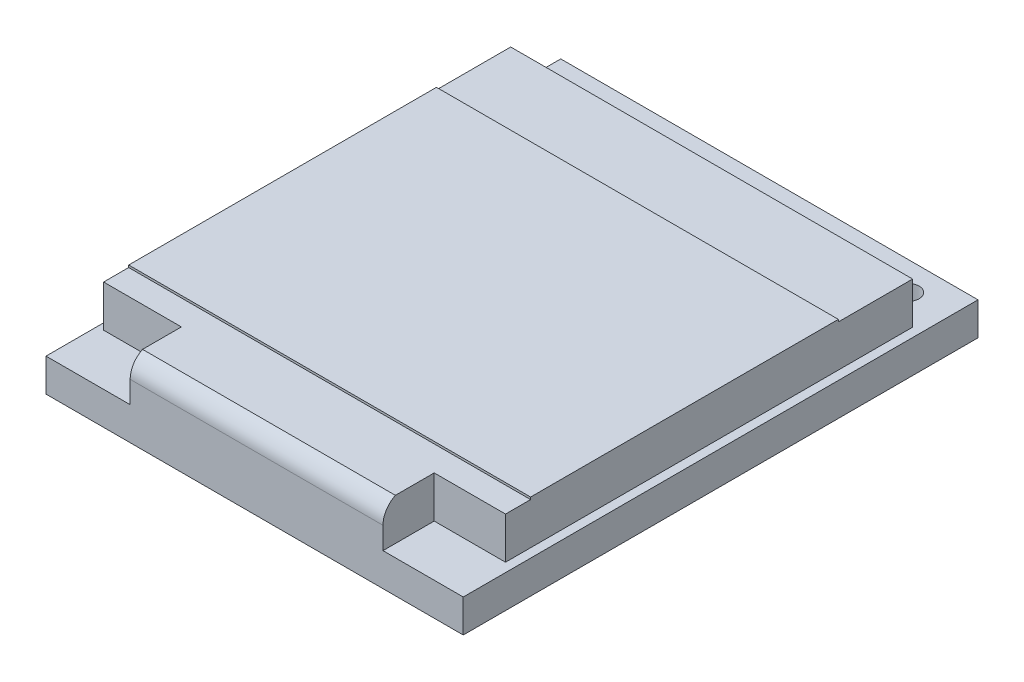
SolidWorks part; units mm, degrees
ref_plane "Front Plane" through (0, 0, 0) normal (0, 0, 1) x (1, 0, 0)
ref_plane "Top Plane" through (0, 0, 0) normal (0, 1, 0) x (1, 0, 0)
ref_plane "Right Plane" through (0, 0, 0) normal (1, 0, 0) x (0, 0, -1)
sketch "Sketch1" plane through (0, 0, 0) normal (0, 1, 0) x (1, 0, 0)
  line L0 (1.88, -1.3) -> (4.42, -1.3) construction
  line L1 (0, 0) -> (19, 0)
  line L2 (0, 0) -> (0, -23.44)
  line L3 (0, -23.44) -> (19, -23.44)
  line L4 (19, 0) -> (19, -23.44)
  circle A0 centre (1.88, -1.3) radius 0.5
  circle A1 centre (4.42, -1.3) radius 0.5
  circle A2 centre (6.96, -1.3) radius 0.5
  circle A3 centre (9.5, -1.3) radius 0.5
  circle A4 centre (12.04, -1.3) radius 0.5
  circle A5 centre (14.58, -1.3) radius 0.5
  circle A6 centre (17.12, -1.3) radius 0.5
  dimension "D3" = 7
  dimension "D5" = 1
  dimension "D1" = 19
  dimension "D2" = 23.44
  dimension "D4" = 2.54
  dimension "D6" = 1.88
  dimension "D7" = 1.3
extrude "Boss-Extrude1" add sketch "Sketch1" along normal blind 1.5
sketch "Sketch3" plane through (0, 1.5, 0) normal (0, 1, 0) x (1, 0, 0)
  line L0 (3.8324, -21.107) -> (3.8324, -23.44)
  line L1 (0.2901, -2.5692) -> (18.5918, -2.5692)
  line L2 (0.2901, -2.5692) -> (0.2901, -21.107)
  line L3 (0.2901, -21.107) -> (3.8324, -21.107)
  line L4 (18.5918, -2.5692) -> (18.5918, -21.107)
  line L5 (0, -23.44) -> (19, -23.44) construction
  line L6 (15.3447, -21.107) -> (15.3447, -23.44)
  line L7 (15.3447, -21.107) -> (18.5918, -21.107)
  line L8 (3.8324, -23.44) -> (15.3447, -23.44)
extrude "Boss-Extrude2" add sketch "Sketch3" along normal blind 2
fillet "Fillet1" radius 1 1 edges at (9.5886, 3.5, 23.44)
sketch "Sketch4" plane through (0, 3.5, 0) normal (0, 1, 0) x (1, 0, 0)
  line L0 (18.5918, -21.107) -> (18.5918, -2.5692) construction
  line L1 (0.2901, -2.5692) -> (18.5918, -2.5692)
  line L2 (0.2901, -2.5692) -> (0.2901, -5.9498)
  line L3 (0.2901, -5.9498) -> (18.5918, -5.9498)
  line L4 (18.5918, -2.5692) -> (18.5918, -5.9498)
  line L5 (0.2901, -2.5692) -> (0.2901, -21.107) construction
  line L6 (18.5918, -19.9645) -> (0.2901, -19.9645)
  line L7 (18.5918, -19.9645) -> (18.5918, -23.44)
  line L8 (18.5918, -23.44) -> (0.2901, -23.44)
  line L9 (0.2901, -19.9645) -> (0.2901, -23.44)
  line L10 (15.3447, -23.44) -> (19, -23.44) construction
extrude "Cut-Extrude1" cut sketch "Sketch4" against normal blind 0.1
